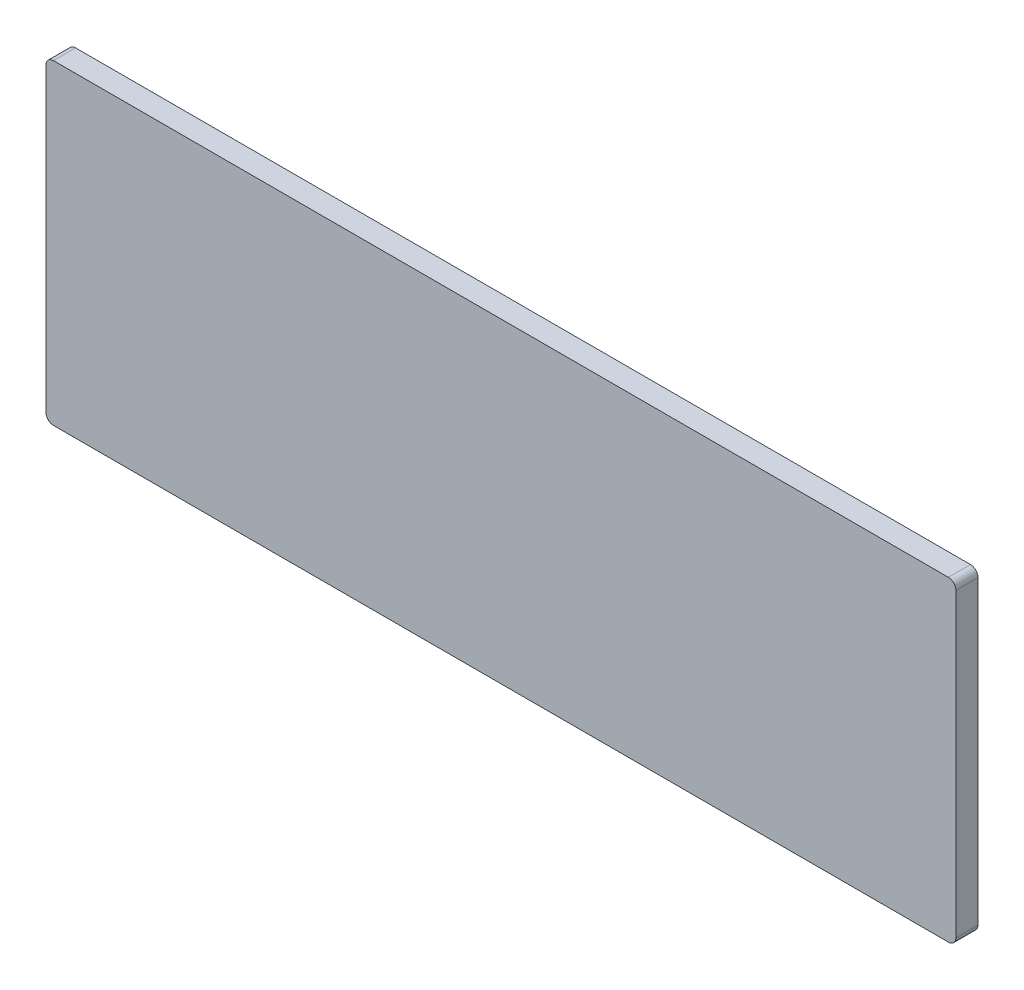
SolidWorks part; units mm, degrees
material "Beech"
ref_plane "Front Plane" through (0, 0, 0) normal (0, 0, 1) x (1, 0, 0)
ref_plane "Top Plane" through (0, 0, 0) normal (0, 1, 0) x (1, 0, 0)
ref_plane "Right Plane" through (0, 0, 0) normal (1, 0, 0) x (0, 0, -1)
sketch "Sketch1" plane through (0, 0, 0) normal (0, 0, 1) x (1, 0, 0)
  line L1 (914.4, 317.5) -> (-914.4, 317.5)
  line L2 (914.4, 317.5) -> (914.4, -317.5)
  line L3 (914.4, -317.5) -> (-914.4, -317.5)
  line L4 (-914.4, 317.5) -> (-914.4, -317.5)
  line L5 (914.4, 317.5) -> (-914.4, -317.5) construction
  line L6 (914.4, -317.5) -> (-914.4, 317.5) construction
  point P0 (0, 0)
  dimension "D1" = 1828.8
  dimension "D2" = 635
extrude "Boss-Extrude1" add sketch "Sketch1" against normal blind 44.45
fillet "Fillet1" radius 15 4 edges at (914.4, -317.5, -22.225) (914.4, 317.5, -22.225) (-914.4, 317.5, -22.225) (-914.4, -317.5, -22.225)
equation "\"altitude_horizontal_rail_length\"=10in"
equation "\"altitude_vertictal_rail_length\"=12in"
equation "\"table_length\"=72in"
equation "\"table_width\"=25in"
equation "\"table_thickness\"=1.75in"
equation "\"D2@Sketch1\"=\"table_width\""
equation "\"D1@Sketch1\"=\"table_length\""
equation "\"D1@Boss-Extrude1\"=\"table_thickness\""
